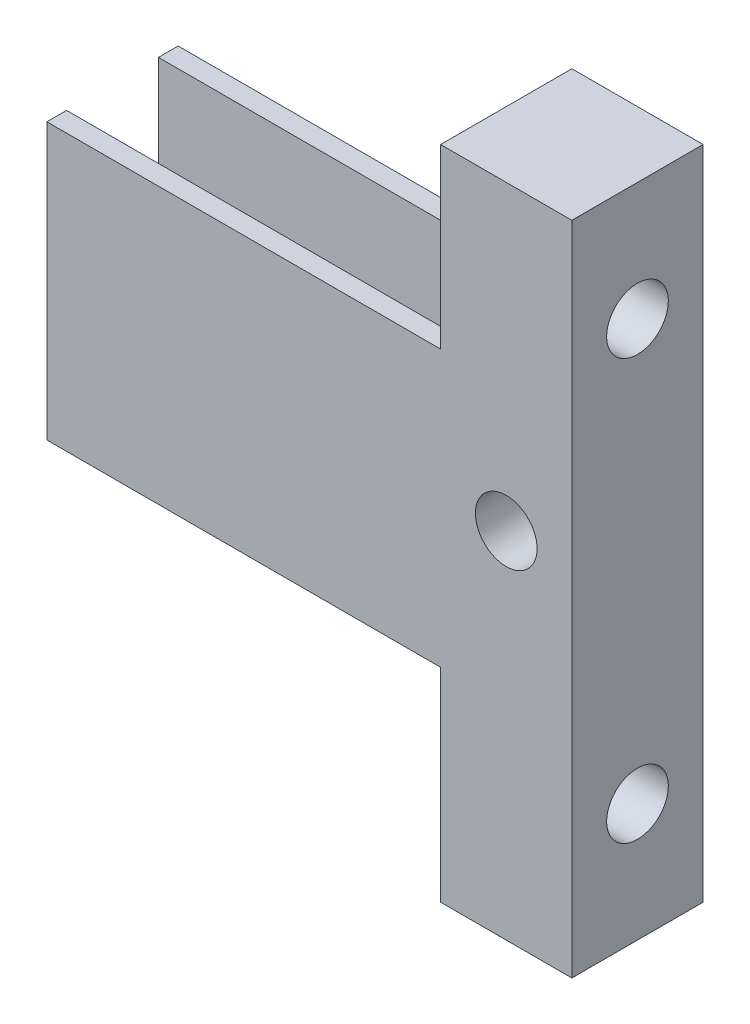
SolidWorks part; units mm, degrees
ref_plane "Front Plane" through (0, 0, 0) normal (0, 0, 1) x (1, 0, 0)
ref_plane "Top Plane" through (0, 0, 0) normal (0, 1, 0) x (1, 0, 0)
ref_plane "Right Plane" through (0, 0, 0) normal (1, 0, 0) x (0, 0, -1)
sketch "Sketch2" plane through (0, 0, 0) normal (0, 0, 1) x (1, 0, 0)
  line L8 (0, 0) -> (0, 50)
  line L9 (0, 50) -> (10, 50)
  line L10 (10, 50) -> (10, 0)
  line L11 (10, 0) -> (0, 0)
  dimension "D1" = 50
  dimension "D2" = 10
extrude "Boss-Extrude1" add sketch "Sketch2" along normal blind 10 contours L11 L8 L9 L10
sketch "Sketch6" plane through (0, 0, 10) normal (0, 0, 1) x (1, 0, 0)
  line L0 (10, 50) -> (10, 0) construction
  line L1 (10, 0) -> (0, 0) construction
  circle A0 centre (5, 27) radius 2.35
  dimension "D1" = 4.7
  dimension "D2" = 5
  dimension "D3" = 27
extrude "Cut-Extrude3" cut sketch "Sketch6" against normal through all contours A0
sketch "Sketch7" plane through (0, 0, 0) normal (-1, 0, 0) x (0, 0, 1)
  line L0 (10, 0) -> (10, 50) construction
  line L1 (10, 0) -> (0, 0) construction
  circle A0 centre (5, 41) radius 2.35
  circle A1 centre (5, 9) radius 2.35
  dimension "D3" = 4.7
  dimension "D4" = 4.7
  dimension "D5" = 9
  dimension "D1" = 32
  dimension "D2" = 5
  dimension "D6" = 5
extrude "Cut-Extrude4" cut sketch "Sketch7" against normal through all
sketch "Sketch8" plane through (0, 0, 0) normal (-1, 0, 0) x (0, 0, 1)
  line L0 (8.5, 36.5) -> (8.5, 15.5)
  line L1 (8.5, 15.5) -> (10, 15.5)
  line L2 (10, 0) -> (10, 50) construction
  line L3 (10, 15.5) -> (10, 36.5)
  line L4 (10, 36.5) -> (8.5, 36.5)
  line L5 (1.5, 36.5) -> (1.5, 15.5)
  line L6 (1.5, 15.5) -> (0, 15.5)
  line L7 (0, 0) -> (0, 50) construction
  line L8 (0, 15.5) -> (0, 36.5)
  line L9 (0, 36.5) -> (1.5, 36.5)
  line L10 (10, 50) -> (0, 50) construction
  dimension "D1" = 1.5
  dimension "D2" = 1.5
  dimension "D3" = 13.5
  dimension "D4" = 21
extrude "Boss-Extrude2" add sketch "Sketch8" along normal blind 30
